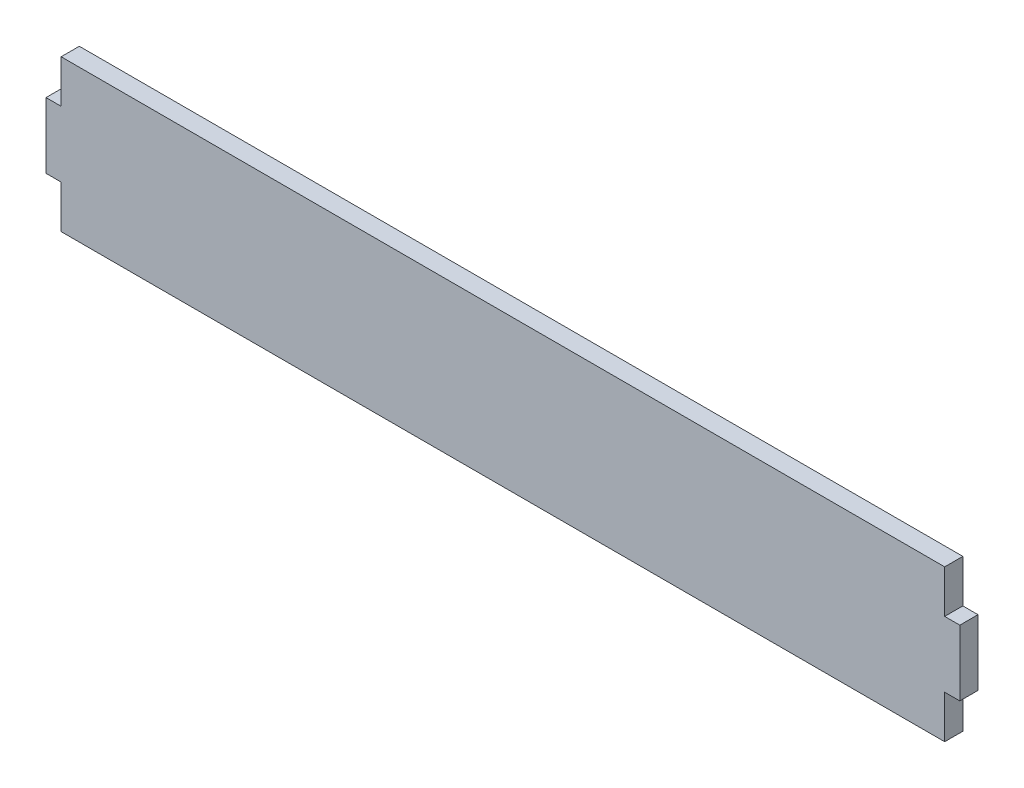
SolidWorks part; units mm, degrees
ref_plane "Front Plane" through (0, 0, 0) normal (0, 0, 1) x (1, 0, 0)
ref_plane "Top Plane" through (0, 0, 0) normal (0, 1, 0) x (1, 0, 0)
ref_plane "Right Plane" through (0, 0, 0) normal (1, 0, 0) x (0, 0, -1)
sketch "Sketch1" plane through (0, 0, 0) normal (0, 0, 1) x (1, 0, 0)
  line L0 (3, 21.5) -> (3, 30)
  line L1 (3, 0) -> (178, 0)
  line L3 (3, 30) -> (178, 30)
  line L5 (0, 21.5) -> (3, 21.5)
  line L6 (0, 21.5) -> (0, 8.5)
  line L7 (0, 8.5) -> (3, 8.5)
  line L10 (0, 0) -> (3, 0) construction
  line L11 (3, 8.5) -> (3, 0)
  line L12 (0, 8.5) -> (0, 0) construction
  line L13 (90.5, 15) -> (90.5, 3.5137) construction
  line L14 (0, 15) -> (181, 15) construction
  line L15 (181, -92.1061) -> (181, 92.2614) construction
  line L16 (178, 8.5) -> (178, 0)
  line L17 (181, 8.5) -> (178, 8.5)
  line L18 (178, 21.5) -> (178, 30)
  line L19 (181, 21.5) -> (178, 21.5)
  line L20 (181, 21.5) -> (181, 8.5)
  dimension "D1" = 30
  dimension "D2" = 13
  dimension "D3" = 3
extrude "Boss-Extrude1" add sketch "Sketch1" along normal blind 3.6
